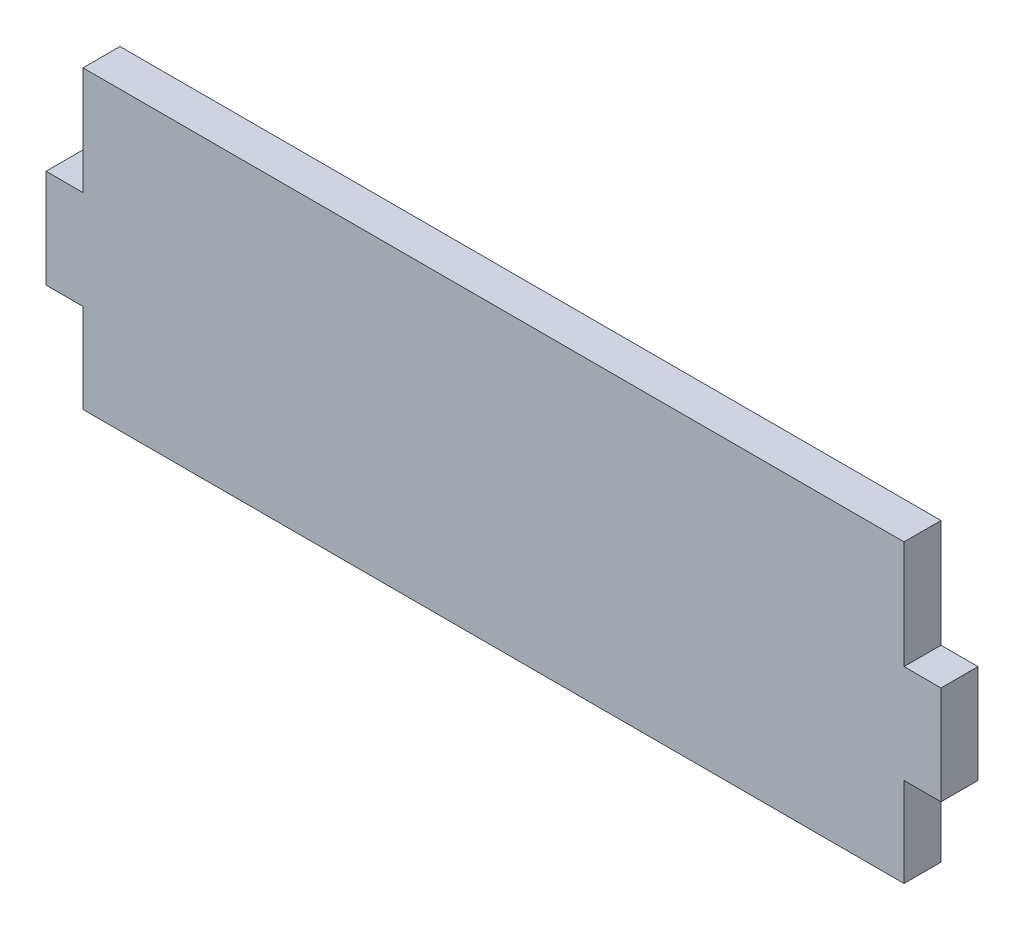
SolidWorks part; units mm, degrees
ref_plane "Alzado" through (0, 0, 0) normal (0, 0, 1) x (1, 0, 0)
ref_plane "Planta" through (0, 0, 0) normal (0, 1, 0) x (1, 0, 0)
ref_plane "Vista lateral" through (0, 0, 0) normal (1, 0, 0) x (0, 0, -1)
sketch "Croquis1" plane through (0, 0, 0) normal (0, 0, 1) x (1, 0, 0)
  line L1 (0, 0) -> (111, 0)
  line L2 (0, 0) -> (0, 40)
  line L3 (0, 40) -> (111, 40)
  line L4 (111, 0) -> (111, 40)
  dimension "D1" = 40
  dimension "D2" = 111
extrude "Saliente-Extruir1" add sketch "Croquis1" along normal blind 5
sketch "Croquis2" plane through (111, 0, 0) normal (1, 0, 0) x (0, 0, -1)
  line L0 (-5, 0) -> (-5, 40) construction
  line L1 (-5, 12.0633) -> (0, 12.0633)
  line L2 (-5, 12.0633) -> (-5, 25.3967)
  line L3 (-5, 25.3967) -> (0, 25.3967)
  line L4 (0, 12.0633) -> (0, 25.3967)
  line L5 (0, 0) -> (0, 40) construction
  line L6 (-5, 0) -> (0, 0) construction
  dimension "D1" = 13.3333
  dimension "D2" = 12.0633
extrude "Saliente-Extruir2" add sketch "Croquis2" along normal blind 5
sketch "Croquis3" plane through (0, 0, 0) normal (-1, 0, 0) x (0, 0, 1)
  line L1 (5, 25.3967) -> (0, 25.3967)
  line L2 (5, 25.3967) -> (5, 12.0633)
  line L3 (5, 12.0633) -> (0, 12.0633)
  line L4 (0, 25.3967) -> (0, 12.0633)
extrude "Saliente-Extruir3" add sketch "Croquis3" along normal blind 5
